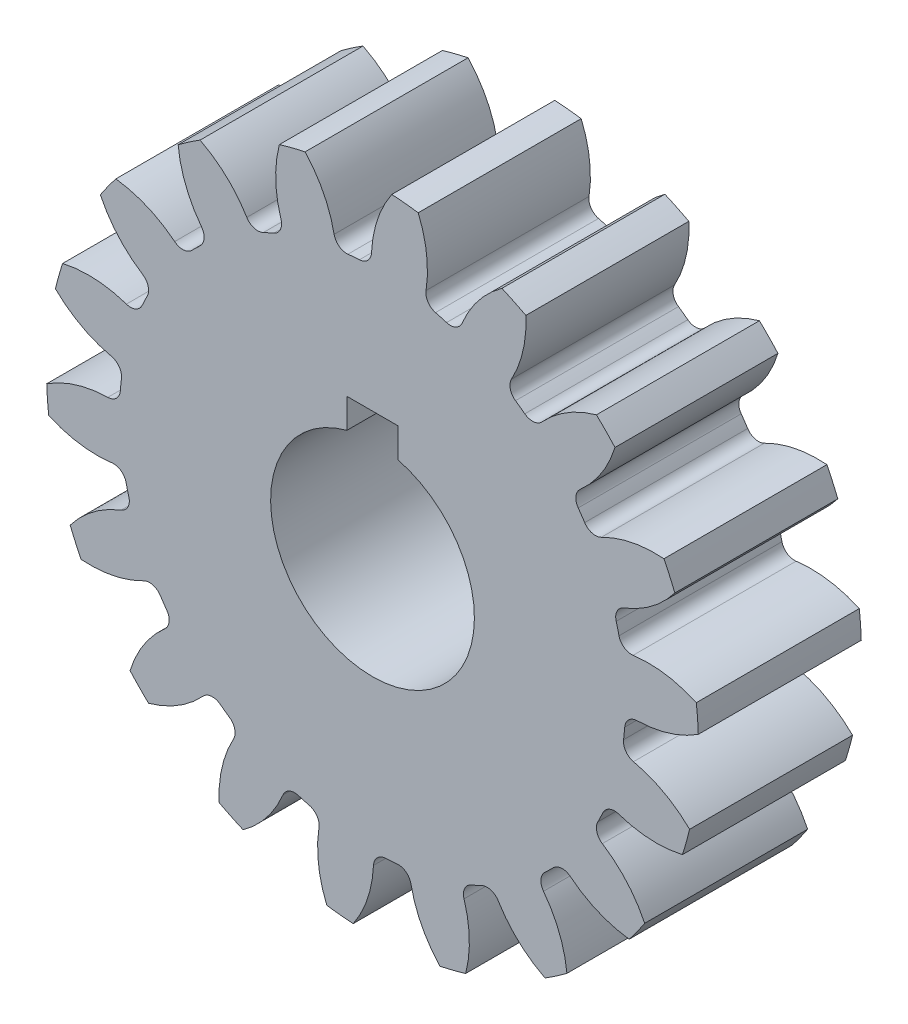
SolidWorks part; units mm, degrees
ref_plane "Front" through (0, 0, 0) normal (0, 0, 1) x (1, 0, 0)
ref_plane "Top" through (0, 0, 0) normal (0, 1, 0) x (1, 0, 0)
ref_plane "Right" through (0, 0, 0) normal (1, 0, 0) x (0, 0, -1)
sketch "Sketch3" plane through (0, 0, 0) normal (0, 0, 1) x (1, 0, 0)
  circle A0 centre (0, 0) radius 12.7
  dimension "od" = 25.4
extrude "gearBody" add sketch "Sketch3" along normal blind 6.35
sketch "Sketch2" plane through (0, 0, 0) normal (0, 0, 1) x (1, 0, 0)
  line L0 (0, 0) -> (10.2236, 4.2347) construction
  line L1 (13.3591, -4.4187) -> (0, 0) construction
  line L2 (0, 0) -> (36.3143, 0) construction
  line L3 (11.4292, -0.1374) -> (11.2291, -2.1338) construction
  line L5 (11.3291, -1.1356) -> (0, 0) construction
  line L7 (0, 0) -> (11.0659, 0) construction
  arc A0 (11.0637, -0.2221) -> (10.8877, -1.9783) centre (0, 0) ccw construction
  arc A1 (12.6927, 0.4305) -> (12.3547, -2.9412) centre (0, 0) ccw construction
  arc A2 (11.4292, -0.1374) -> (11.2291, -2.1338) centre (0, 0) ccw construction
  arc A3 (9.7812, -1.2052) -> (9.8258, -0.7602) centre (0, 0) ccw
  arc A4 (13.3591, -4.4187) -> (10.1678, -1.7534) centre (9.1796, -6.1797) ccw
  arc A5 (13.3591, -4.4187) -> (13.9704, 1.6792) centre (0, 0) ccw
  arc A6 (13.9704, 1.6792) -> (10.3136, -0.2997) centre (10.2236, 4.2347) cw
  arc A7 (9.8258, -0.7602) -> (10.3136, -0.2997) centre (10.3235, -0.7987) cw
  arc A8 (10.1678, -1.7534) -> (9.7812, -1.2052) centre (10.2766, -1.2662) cw
  point P6 (13.9704, 1.6792)
  point P22 (13.3591, -4.4187)
  dimension "baseDia" = 22.1319
  dimension "od" = 25.4
  dimension "pd" = 22.86
  dimension "rd" = 19.7104
  dimension "rFillet" = 0.4991
  dimension "pointX" = 13.9704
  dimension "pointY" = 1.6792
  dimension "CTT" = 1.9964
  dimension "flankCenterAngle" = 22.5
extrude "toothCut" cut sketch "Sketch2" along normal through all
pattern_circular "CirPattern1" count 18 over 360 about axis through (0, 0, 0) along (0, 0, 1) of "toothCut"
sketch "hub1Dia" plane through (0, 0, 0) normal (0, 0, -1) x (-1, 0, 0)
  circle A0 centre (0, 0) radius 25.4
  dimension "hub1Dia" = 50.8
extrude "hub1" [suppressed] add sketch "hub1Dia" along normal blind 19.05
sketch "hub2Dia" plane through (0, 0, 6.35) normal (0, 0, 1) x (1, 0, 0)
  circle A0 centre (0, 0) radius 21.844
  dimension "hub2dia" = 43.688
extrude "hub2" [suppressed] add sketch "hub2Dia" along normal blind 16.002
sketch "boreDia" plane through (0, 0, 0) normal (0, 0, 1) x (1, 0, 0)
  line L1 (-1, 3.842) -> (-1, 4.9926)
  line L2 (1, 3.842) -> (1, 4.9926)
  line L3 (-1, 4.9926) -> (1, 4.9926)
  arc A0 (-1, 3.842) -> (1, 3.842) centre (0, 0) ccw
  dimension "D1" = 2
  dimension "boreDia" = 7.94
  dimension "D2" = 1.1506
extrude "bore" cut sketch "boreDia" against normal mid plane 25.4
chamfer "hub2Chamfer" [suppressed] distance 0.508 angle 45
chamfer "hub2BoreChamfer" [suppressed] distance 0.508 angle 45
chamfer "hub1BoreChamfer" [suppressed] distance 0.508 angle 45
chamfer "hub1Chamfer" [suppressed] distance 0.508 angle 45
chamfer "BoreChamfer2" [suppressed] distance 0.508 angle 45
chamfer "boreChamfer1" [suppressed] distance 0.508 angle 45
